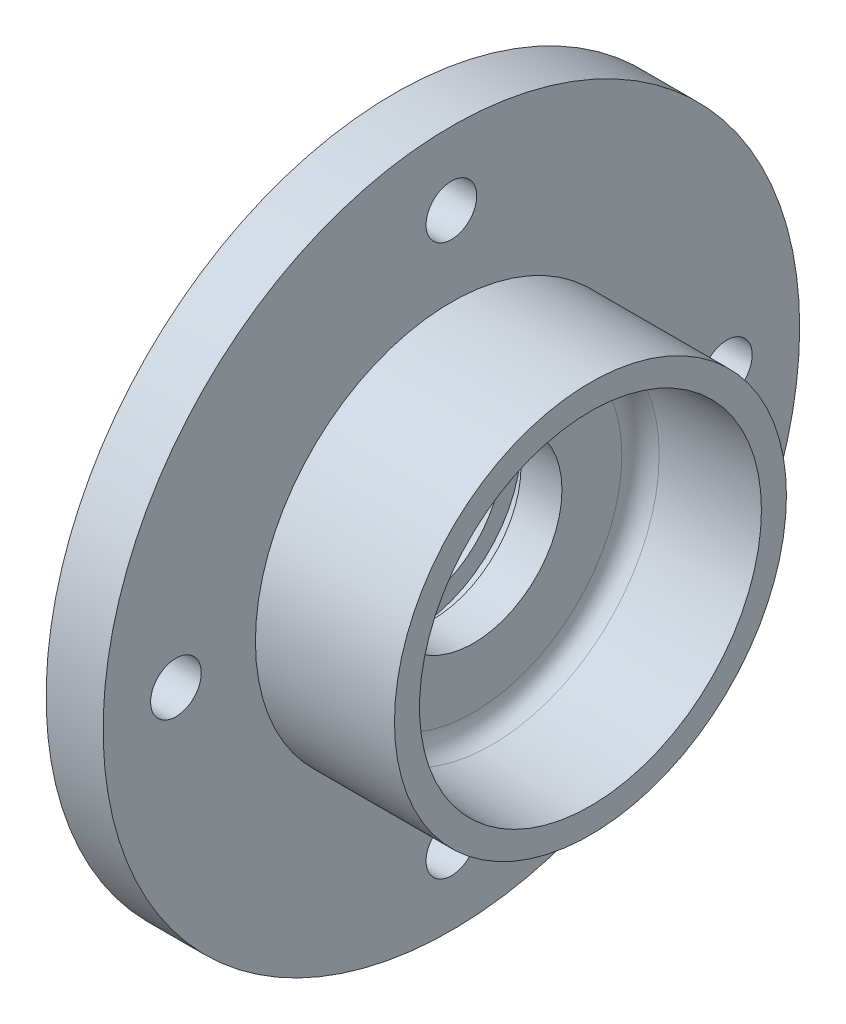
SolidWorks part; units mm, degrees
ref_plane "前视基准面" through (0, 0, 0) normal (0, 0, 1) x (1, 0, 0)
ref_plane "上视基准面" through (0, 0, 0) normal (0, 1, 0) x (1, 0, 0)
ref_plane "右视基准面" through (0, 0, 0) normal (1, 0, 0) x (0, 0, -1)
sketch "草图1" plane through (0, 0, 0) normal (1, 0, 0) x (0, 0, -1)
  circle A0 centre (0, 0) radius 55
extrude "凸台-拉伸1" add sketch "草图1" along normal blind 9
sketch "草图2" plane through (9, 0, 0) normal (1, 0, 0) x (0, 0, -1)
  circle A0 centre (0, 0) radius 30.95
extrude "凸台-拉伸2" add sketch "草图2" along normal blind 21.96
sketch "草图3" plane through (30.96, 0, 0) normal (1, 0, 0) x (0, 0, -1)
  circle A0 centre (0, 0) radius 27
extrude "切除-拉伸1" cut sketch "草图3" against normal blind 18.5 draft 2
fillet "圆角1" radius 3 1 edges at (12.46, 0, -26.354)
sketch "草图4" plane through (12.46, 0, 0) normal (1, 0, 0) x (0, 0, -1)
  circle A0 centre (0, 0) radius 14
extrude "切除-拉伸2" cut sketch "草图4" against normal blind 18.5
sketch "草图5" plane through (0, 0, 0) normal (0, 1, 0) x (1, 0, 0)
  line L4 (3, -11) -> (6, -11)
  line L5 (3, -11) -> (3, -17)
  line L6 (3, -17) -> (6, -17)
  line L7 (6, -11) -> (6, -17)
  point P7 (4.5, -14)
  dimension "D1" = 3
  dimension "D2" = 6
ref_plane "基准面1" through (4.5, 0, 14) normal (1, 0, 0) x (0, 0, -1)
sketch "草图6" plane through (4.5, 0, 14) normal (1, 0, 0) x (0, 0, -1)
  circle A0 centre (14, 0) radius 14
sweep "切除-扫描1" cut profiles "草图5" path "草图6"
sketch "草图7" plane through (0, 0, 0) normal (-1, 0, 0) x (0, 0, 1)
  circle A0 centre (0, 0) radius 32
extrude "切除-拉伸3" cut sketch "草图7" against normal blind 1
sketch "草图8" plane through (0, 0, 0) normal (-1, 0, 0) x (0, 0, 1)
  line L0 (0, 32) -> (0, 55)
  line L1 (32, 0) -> (55, 0)
  line L2 (0, -55) -> (0, -32)
  line L3 (-55, 0) -> (-32, 0)
  circle A0 centre (0, 0) radius 32 construction
  circle A1 centre (0, 0) radius 55 construction
  circle A2 centre (43.5, 0) radius 4
  circle A3 centre (0, -43.5) radius 4
  circle A4 centre (-43.5, 0) radius 4
  circle A5 centre (0, 43.5) radius 4
  dimension "D1" = 8
  dimension "D2" = 8
  dimension "D3" = 8
  dimension "D4" = 8
extrude "切除-拉伸4" cut sketch "草图8" against normal blind 20 contours L0 A5 | L0 A5 | L1 A2 | L1 A2 | L2 A3 | L2 A3 | L3 A4 | L3 A4
